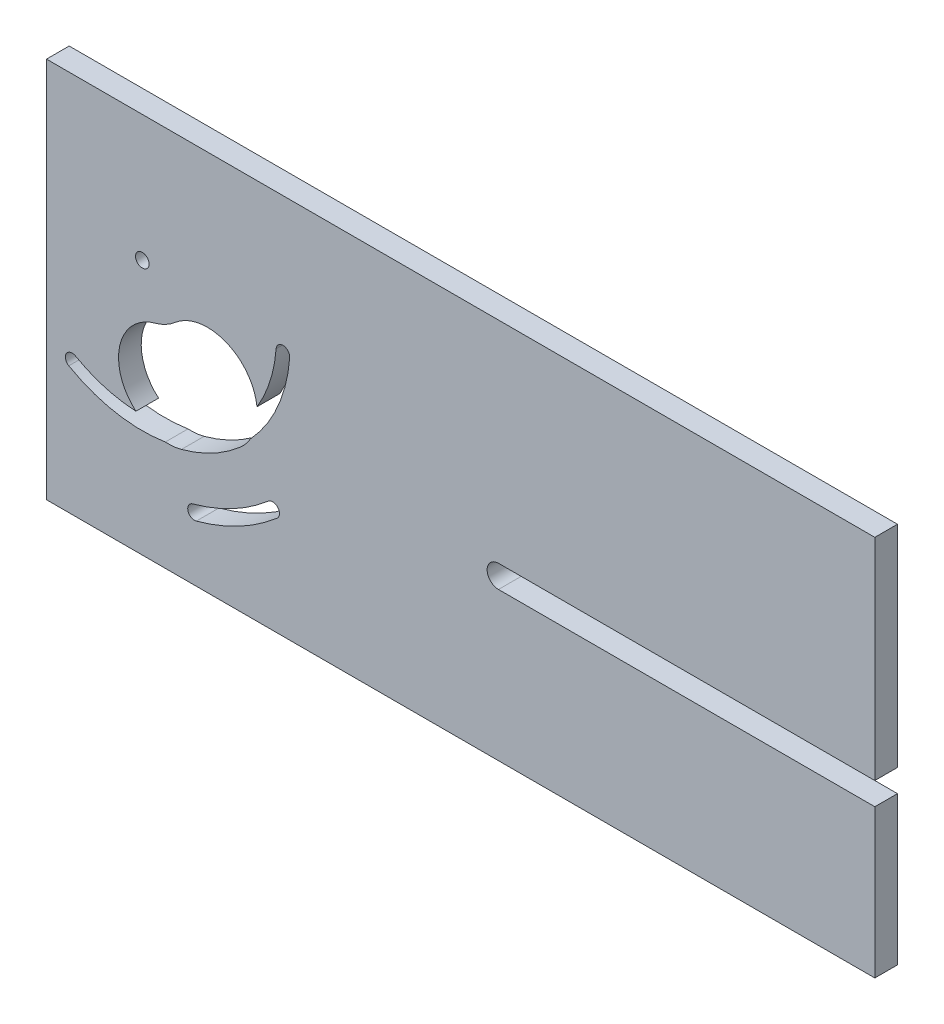
SolidWorks part; units mm, degrees
ref_plane "Front" through (0, 0, 0) normal (0, 0, 1) x (1, 0, 0)
ref_plane "Top" through (0, 0, 0) normal (0, 1, 0) x (1, 0, 0)
ref_plane "Right" through (0, 0, 0) normal (1, 0, 0) x (0, 0, -1)
sketch "Sketch1" plane through (0, 0, 0) normal (0, 0, 1) x (1, 0, 0)
  line L0 (-70.2236, 14.2507) -> (-39.2061, 11.9862) construction
  line L1 (-91.35, -42.09) -> (91.35, -42.09)
  line L2 (-91.35, -42.09) -> (-91.35, 42.09)
  line L3 (-91.35, 42.09) -> (91.35, 42.09)
  line L4 (91.35, -42.09) -> (91.35, 42.09)
  line L5 (-91.35, -42.09) -> (91.35, 42.09) construction
  line L6 (-91.35, 42.09) -> (91.35, -42.09) construction
  line L7 (-75.8236, -22.4493) -> (-33.5236, -22.4493) construction
  line L8 (-75.8236, -22.4493) -> (-75.8236, 19.8507) construction
  line L9 (-75.8236, 19.8507) -> (-33.5236, 19.8507) construction
  line L10 (-33.5236, -22.4493) -> (-33.5236, 19.8507) construction
  line L11 (-75.8236, -22.4493) -> (-33.5236, 19.8507) construction
  line L12 (-75.8236, 19.8507) -> (-33.5236, -22.4493) construction
  line L13 (-70.2236, -16.8493) -> (-39.1236, -16.8493) construction
  line L14 (-70.2236, -16.8493) -> (-70.2236, 14.2507) construction
  line L15 (-70.2236, 14.2507) -> (-39.1236, 14.2507) construction
  line L16 (-39.1236, -16.8493) -> (-39.1236, 14.2507) construction
  line L17 (-70.2236, -16.8493) -> (-39.1236, 14.2507) construction
  line L18 (-70.2236, 14.2507) -> (-39.1236, -16.8493) construction
  line L19 (-70.2236, 14.2507) -> (-85.6857, -12.7332) construction
  line L20 (-70.2236, 14.2507) -> (-58.7018, -28.1954) construction
  line L21 (-70.2236, 14.2507) -> (-41.4706, -19.0312) construction
  line L22 (-81.35, 48.3317) -> (101.35, 48.3317) construction
  line L23 (8.3431, -4.3738) -> (91.35, -4.3738)
  line L24 (8.3431, -9.3738) -> (91.35, -9.3738)
  arc A0 (8.3431, -4.3738) -> (8.3431, -9.3738) centre (8.3431, -6.8738) ccw
  circle A1 centre (-39.1236, 14.2507) radius 1.5 construction
  circle A2 centre (-70.2236, 14.2507) radius 1.5
  circle A3 centre (-70.2236, -16.8493) radius 1.5 construction
  circle A4 centre (-39.1236, -16.8493) radius 1.5 construction
  circle A5 centre (-70.2236, 14.2507) radius 31.1 construction
  circle A6 centre (-70.2236, 14.2507) radius 43.982 construction
  arc A7 (-86.4315, -14.0347) -> (-65.1444, -17.9512) centre (-70.2236, 14.2507) ccw
  arc A8 (-58.3088, -29.643) -> (-40.49, -20.1663) centre (-70.2236, 14.2507) ccw
  arc A9 (-84.9399, -11.4318) -> (-71.6311, -15.3158) centre (-70.2236, 14.2507) ccw
  arc A10 (-59.0947, -26.7478) -> (-42.4512, -17.8962) centre (-70.2236, 14.2507) ccw
  circle A11 centre (-39.2061, 11.9862) radius 1.5
  circle A12 centre (-41.4706, -19.0312) radius 1.5
  circle A13 centre (-85.6857, -12.7332) radius 1.5
  circle A14 centre (-58.7018, -28.1954) radius 1.5
  circle A15 centre (-70.2236, 14.2507) radius 29.6 construction
  circle A16 centre (-70.2236, 14.2507) radius 32.6 construction
  circle A17 centre (-70.2236, 14.2507) radius 42.482 construction
  circle A18 centre (-70.2236, 14.2507) radius 45.482 construction
  circle A19 centre (8.3431, -6.8738) radius 2.5 construction
  circle A20 centre (-70.2236, 14.2507) radius 21.991 construction
  arc A21 (-63.0383, 5.9336) -> (-44.9217, -1.1109) centre (-55.8471, -2.3903) cw
  arc A22 (-67.3443, 3.6435) -> (-71.6311, -15.3158) centre (-64.4627, -6.9723) ccw
  arc A23 (-67.3443, 3.6435) -> (-63.0383, 5.9336) centre (-70.2236, 14.2507) ccw
  arc A24 (-44.9217, -1.1109) -> (-40.7021, 12.0954) centre (-70.2236, 14.2507) ccw
  arc A25 (-61.581, -17.5882) -> (-48.6559, -10.7141) centre (-70.2236, 14.2507) ccw
  arc A26 (-46.3629, -7.9626) -> (-37.7101, 11.877) centre (-70.2236, 14.2507) ccw
  arc A27 (-46.3629, -7.9626) -> (-48.6559, -10.7141) centre (-55.8471, -2.3903) cw
  arc A28 (-65.1444, -17.9512) -> (-61.581, -17.5882) centre (-64.4627, -6.9723) ccw
  point P0 (0, 0)
  point P8 (-54.6736, -1.2993)
  point P13 (-54.6736, -1.2993)
  dimension "D2" = 3
  dimension "D8" = 11
  dimension "D1" = 31.1
  dimension "D3" = 42.3
  dimension "D6" = 45
  dimension "D7" = 45
  dimension "D9" = 84.18
  dimension "D4" = 1.5
  dimension "D5" = 1.5
extrude "Boss-Extrude1" add sketch "Sketch1" along normal blind 5 contours L1 L4 L3 L2 A14 A10 A12 A8 A0 A13 A9 A11 A7
